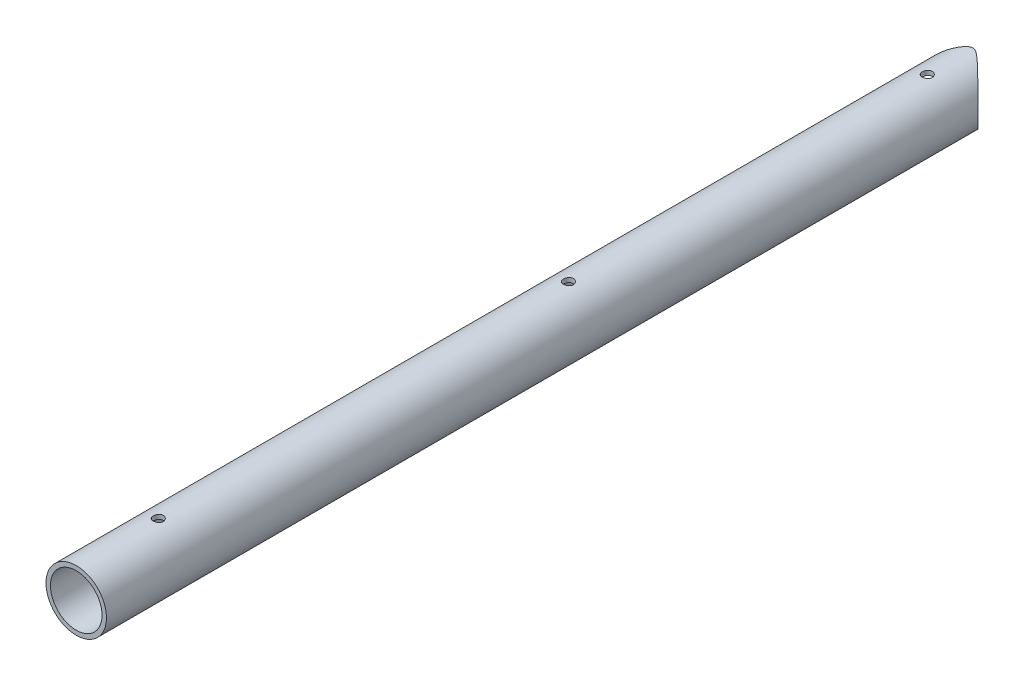
SolidWorks part; units mm, degrees
ref_plane "Front" through (0, 0, 0) normal (0, 0, 1) x (1, 0, 0)
ref_plane "Top" through (0, 0, 0) normal (0, 1, 0) x (1, 0, 0)
ref_plane "Right" through (0, 0, 0) normal (1, 0, 0) x (0, 0, -1)
sketch "Sketch1" plane through (0, 0, 0) normal (0, 0, 1) x (1, 0, 0)
  circle A0 centre (0, 0) radius 9.36
  circle A1 centre (0, 0) radius 7.99
extrude "Extrude1" add sketch "Sketch1" along normal blind 279.4
sketch "Sketch2" plane through (0, 0, 0) normal (1, 0, 0) x (0, 0, -1)
  circle A0 centre (0, 0) radius 9.525
extrude "Cut-Extrude1" cut sketch "Sketch2" against normal through all and the other way through all
sketch "Sketch3" plane through (0, 0, 0) normal (0, 1, 0) x (1, 0, 0)
  line L0 (0, -279.4) -> (0, -9.5246) construction
  line L1 (0, -279.4) -> (0, -9.5246) construction
  circle A0 centre (0, -15.88) radius 1.55
  circle A1 centre (0, -127) radius 1.55
  circle A2 centre (0, -254) radius 1.55
extrude "Cut-Extrude2" cut sketch "Sketch3" against normal through all and the other way through all
sketch "Sketch4" plane through (0, 0, 0) normal (1, 0, 0) x (0, 0, -1)
  line L0 (-279.4, 0) -> (-9.5246, 0) construction
  circle A0 centre (-127, 0) radius 3.5
  circle A1 centre (-254, 0) radius 3.5
extrude "Cut-Extrude3" cut sketch "Sketch4" against normal through all
